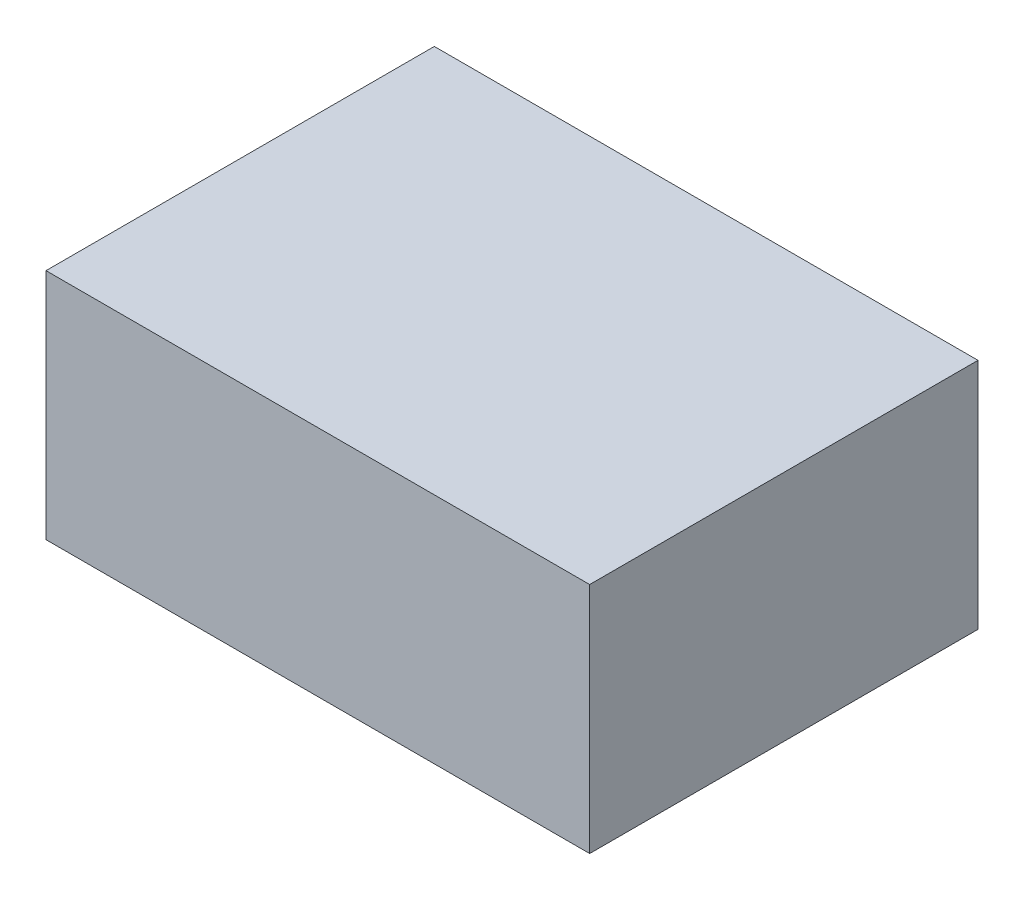
SolidWorks part; units mm, degrees
ref_plane "Front Plane" through (0, 0, 0) normal (0, 0, 1) x (1, 0, 0)
ref_plane "Top Plane" through (0, 0, 0) normal (0, 1, 0) x (1, 0, 0)
ref_plane "Right Plane" through (0, 0, 0) normal (1, 0, 0) x (0, 0, -1)
sketch "Sketch1" plane through (0, 0, 0) normal (0, 1, 0) x (1, 0, 0)
  line L1 (17.6214, -31.0998) -> (-52.3786, -31.0998)
  line L2 (17.6214, -31.0998) -> (17.6214, 18.9002)
  line L3 (17.6214, 18.9002) -> (-52.3786, 18.9002)
  line L4 (-52.3786, -31.0998) -> (-52.3786, 18.9002)
extrude "Boss-Extrude1" add sketch "Sketch1" along normal blind 30
